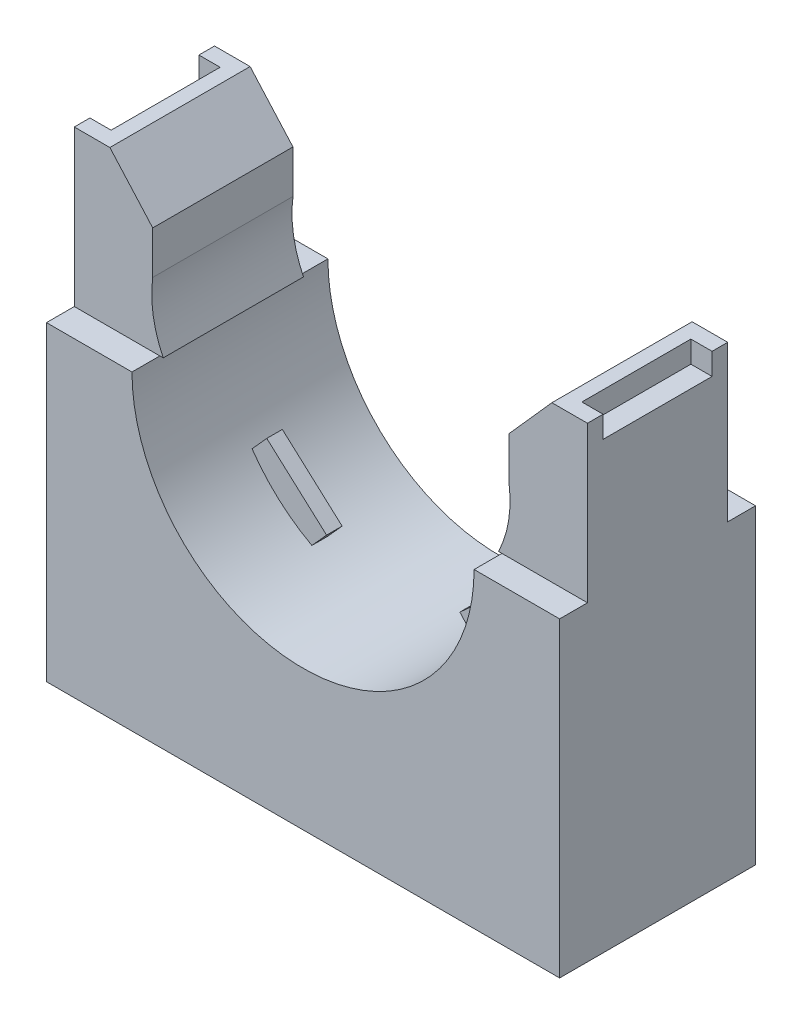
SolidWorks part; units mm, degrees
ref_plane "Front Plane" through (0, 0, 0) normal (0, 0, 1) x (1, 0, 0)
ref_plane "Top Plane" through (0, 0, 0) normal (0, 1, 0) x (1, 0, 0)
ref_plane "Right Plane" through (0, 0, 0) normal (1, 0, 0) x (0, 0, -1)
sketch "Sketch1" plane through (0, 0, 0) normal (0, 0, 1) x (1, 0, 0)
  line L0 (-20.955, -19.05) -> (20.955, 19.05) construction
  line L1 (-20.955, 19.05) -> (20.955, 19.05)
  line L2 (-20.955, 19.05) -> (-20.955, -19.05)
  line L3 (-20.955, -19.05) -> (20.955, -19.05)
  line L4 (20.955, 19.05) -> (20.955, -19.05)
  arc A0 (-13.6884, 3.5591) -> (13.6932, 3.583) centre (0, 6.35) ccw construction
  point P4 (0, 0)
  dimension "D3" = 25.4
  dimension "D4" = 13.97
  dimension "B" = 41.91
  dimension "C" = 38.1
extrude "Extrude1" add sketch "Sketch1" along normal blind 16.002
sketch "Sketch2" plane through (0, 0, 16.002) normal (0, 0, 1) x (1, 0, 0)
  line L1 (-13.97, 6.35) -> (-13.6906, 6.35)
  line L2 (13.6906, 6.35) -> (13.97, 6.35)
  line L3 (14.5494, 11.6126) -> (14.5494, 15.113)
  line L4 (14.5494, 15.113) -> (18.0499, 19.05)
  line L5 (20.955, 19.05) -> (-20.955, 19.05) construction
  line L6 (0, 0) -> (0, 22.8281) construction
  line L7 (-14.5494, 15.113) -> (-18.0499, 19.05)
  line L8 (-14.5494, 11.6126) -> (-14.5494, 15.113)
  line L9 (18.0499, 19.05) -> (-18.0499, 19.05)
  line L10 (20.955, -19.05) -> (20.955, 19.05) construction
  arc A0 (-13.97, 6.35) -> (13.97, 6.35) centre (0, 6.35) ccw
  arc A1 (14.5494, 11.6126) -> (13.6906, 6.35) centre (5.4957, 10.3887) cw
  arc A2 (-14.5494, 11.6126) -> (-13.6906, 6.35) centre (-5.4957, 10.3887) ccw
  arc A3 (-13.6884, 3.5591) -> (13.6932, 3.583) centre (0, 6.35) ccw construction
  dimension "D1" = 0.2794
  dimension "D3" = 9.1361
  dimension "D2" = 3.5004
  dimension "D4" = 3.5004
  dimension "D7" = 6.4056
  dimension "D8" = 5.2626
extrude "Cut-Extrude1" cut sketch "Sketch2" against normal through all
sketch "Sketch3" plane through (0, 0, 0) normal (1, 0, 0) x (0, 0, -1)
  line L1 (-16.002, 6.35) -> (-13.7274, 6.35)
  line L2 (-13.7274, 19.05) -> (-13.7274, 6.35)
  line L3 (-16.002, 6.35) -> (-16.002, 19.05)
  line L4 (-2.2746, 19.05) -> (-2.2746, 6.35)
  line L5 (-8.001, 31.6865) -> (-8.001, 10.4775) construction
  line L6 (-16.002, 19.05) -> (0, 19.05) construction
  line L7 (-16.002, -19.05) -> (-16.002, 19.05) construction
  line L8 (-16.002, 19.05) -> (-13.7274, 19.05)
  line L9 (0, 6.35) -> (0, 19.05)
  line L10 (0, 6.35) -> (-2.2746, 6.35)
  line L11 (-2.2746, 19.05) -> (0, 19.05)
  line L13 (0, -19.05) -> (0, 19.05) construction
  dimension "D2" = 2.2746
extrude "Cut-Extrude2" cut sketch "Sketch3" against normal through all and the other way through all
sketch "Sketch4" plane through (0, -19.05, 0) normal (0, -1, 0) x (1, 0, 0)
  line L12 (-20.955, 15.2082) -> (20.955, 15.2082)
  line L13 (-20.1613, 15.2082) -> (20.1612, 15.2082)
  line L14 (-20.1613, 0.7937) -> (-20.1613, 16.002)
  line L15 (20.1612, 0.7937) -> (-20.1613, 0.7937)
  line L16 (20.1612, 16.002) -> (20.1612, 0.7937)
  line L17 (-20.1613, 0.7937) -> (-20.1613, 15.2082)
  line L18 (20.1612, 0.7937) -> (-20.1613, 0.7937)
  line L19 (20.1612, 15.2082) -> (20.1612, 0.7937)
  dimension "D1" = 0.7937
  dimension "D2" = 0.7937
extrude "Cut-Extrude3" cut sketch "Sketch4" against normal blind 0.254
sketch "Sketch5" plane through (0, 19.05, 0) normal (0, 1, 0) x (1, 0, 0)
  line L0 (-20.955, -2.2746) -> (-18.0499, -2.2746) construction
  line L2 (-20.955, -3.5503) -> (-19.2236, -3.5503)
  line L3 (-20.955, -3.5503) -> (-20.955, -12.4517)
  line L4 (-20.955, -12.4517) -> (-19.2236, -12.4517)
  line L6 (-19.2236, -3.5503) -> (-19.2236, -12.4517)
  line L10 (20.955, -3.5503) -> (19.2236, -3.5503)
  line L11 (20.955, -3.5503) -> (20.955, -12.4517)
  line L12 (20.955, -12.4517) -> (19.2236, -12.4517)
  line L13 (19.2236, -3.5503) -> (19.2236, -12.4517)
  line L14 (20.955, -13.7274) -> (20.955, -2.2746) construction
  line L15 (-20.955, -13.7274) -> (-20.955, -2.2746) construction
  line L16 (18.0499, -8.001) -> (-18.0499, -8.001) construction
  line L17 (18.0499, -2.2746) -> (18.0499, -13.7274) construction
  line L18 (-18.0499, -2.2746) -> (-18.0499, -13.7274) construction
  dimension "D1" = 1.2757
  dimension "D2" = 1.1737
extrude "Cut-Extrude4" cut sketch "Sketch5" against normal blind 1.778
ref_plane "Plane1" through (0, 0, 8.001) normal (0, 0, -1) x (-1, 0, 0)
sketch "Sketch6" plane through (0, 0, 8.001) normal (0, 0, -1) x (-1, 0, 0)
  line L0 (0, 0) -> (0, -34.0604) construction
  line L1 (3.25, -18.796) -> (0, -18.796)
  line L2 (20.1613, -18.796) -> (-20.1612, -18.796) construction
  line L3 (0, -12.296) -> (5.842, -12.296)
  line L4 (5.842, -12.296) -> (5.842, -15.546)
  line L5 (5.842, -15.546) -> (3.25, -15.546)
  line L6 (3.25, -15.546) -> (3.25, -18.796)
  line L7 (0, -18.796) -> (0, -12.296)
  dimension "E" = 11.684
  dimension "D" = 6.5
  dimension "D3" = 3.25
  dimension "D4" = 6.5
revolve "Cut-Revolve1" cut sketch "Sketch6" angle 360 about L0
sketch "Sketch7" plane through (0, 0, 8.001) normal (0, 0, -1) x (-1, 0, 0)
  line L0 (0, 16.5622) -> (0, -24.4387) construction
  line L1 (0, 6.35) -> (7.8851, -2.4073) construction
  line L2 (5.4431, -4.6062) -> (10.3272, -0.2085)
  line L3 (10.3272, -0.2085) -> (11.5275, -1.5416)
  line L4 (5.4431, -4.6062) -> (6.6434, -5.9393)
  line L5 (-5.4431, -4.6062) -> (-6.6434, -5.9393)
  line L6 (-10.3272, -0.2085) -> (-11.5275, -1.5416)
  line L7 (-5.4431, -4.6062) -> (-10.3272, -0.2085)
  arc A0 (-13.6932, 3.583) -> (13.6884, 3.5591) centre (0, 6.35) ccw construction
  arc A3 (6.6434, -5.9393) -> (11.5275, -1.5416) centre (0, 6.35) ccw
  arc A4 (-6.6434, -5.9393) -> (-11.5275, -1.5416) centre (0, 6.35) cw
  point P9 (7.8851, -2.4073)
  dimension "D1" = 42
  dimension "D2" = 6.5722
  dimension "D3" = 1.7939
extrude "Extrude2" add sketch "Sketch7" along normal mid plane 1.27
equation "\"D3@Sketch1\" = (\"C@Sketch1\"/3)*2"
equation "\"D4@Sketch1\" = \"B@Sketch1\"/3"
equation "\"D3@Sketch2\" = ((\"D4@Sketch1\"/4)*3)+0.0146875"
equation "\"D8@Sketch2\" = (\"D3@Sketch2\"/2)+0.02734375"
equation "\"D4@Sketch2\" = ((\"D8@Sketch2\"/4)*3)-0.009765625-0.0078125"
equation "\"D7@Sketch2\" = (\"D4@Sketch2\"*2)-0.0234375"
equation "\"D2@Sketch7\" = (\"D4@Sketch1\"/2)-0.01625"
equation "\"D3@Sketch7\" = \"D2@Sketch7\"/3-0.015625"
equation "\"D2@Sketch2\" = \"D4@Sketch2\""
equation "\"D1@Sketch2\" = \"D4@Sketch1\"/50"
equation "\"D4@Sketch6\" = \"D@Sketch6\""
equation "\"D3@Sketch6\" = \"D4@Sketch6\"/2"
